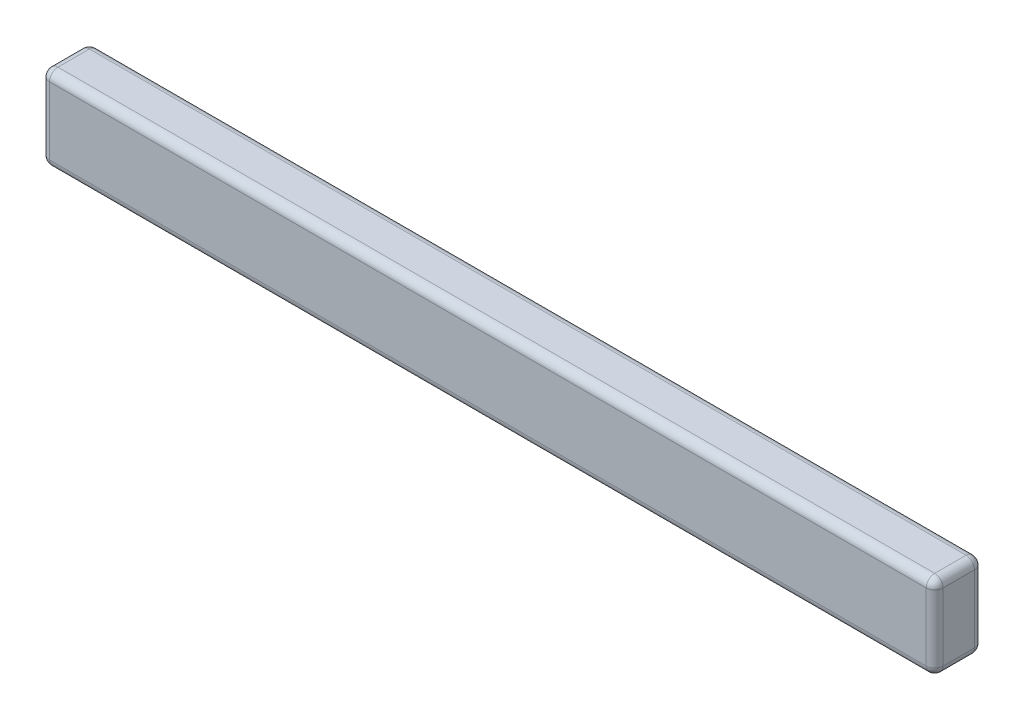
SolidWorks part; units mm, degrees
ref_plane "Front Plane" through (0, 0, 0) normal (0, 0, 1) x (1, 0, 0)
ref_plane "Top Plane" through (0, 0, 0) normal (0, 1, 0) x (1, 0, 0)
ref_plane "Right Plane" through (0, 0, 0) normal (1, 0, 0) x (0, 0, -1)
sketch "Sketch1" plane through (0, 0, 0) normal (0, 0, 1) x (1, 0, 0)
  line L1 (-1300.1605, -324.547) -> (2399.8395, -324.547)
  line L2 (-1300.1605, -324.547) -> (-1300.1605, -674.547)
  line L3 (-1300.1605, -674.547) -> (2399.8395, -674.547)
  line L4 (2399.8395, -324.547) -> (2399.8395, -674.547)
  line L5 (-1300.1605, -324.547) -> (2399.8395, -674.547) construction
  line L6 (-1300.1605, -674.547) -> (2399.8395, -324.547) construction
  point P0 (0, 0)
  point P5 (2197.6417, 845.9677)
  point P6 (2399.8395, -674.547)
  dimension "D1" = 350
  dimension "D2" = 3700
extrude "Boss-Extrude2" add sketch "Sketch1" along normal blind 200
fillet "Fillet1" radius 35 12 edges at (2399.8395, -324.547, 100) (-1300.1605, -324.547, 100) (-1300.1605, -674.547, 100) (2399.8395, -674.547, 100) (549.8395, -674.547, 200) (-1300.1605, -499.547, 200) (549.8395, -324.547, 200) (2399.8395, -499.547, 200) (549.8395, -324.547, 0) (-1300.1605, -499.547, 0) (549.8395, -674.547, 0) (2399.8395, -499.547, 0)
